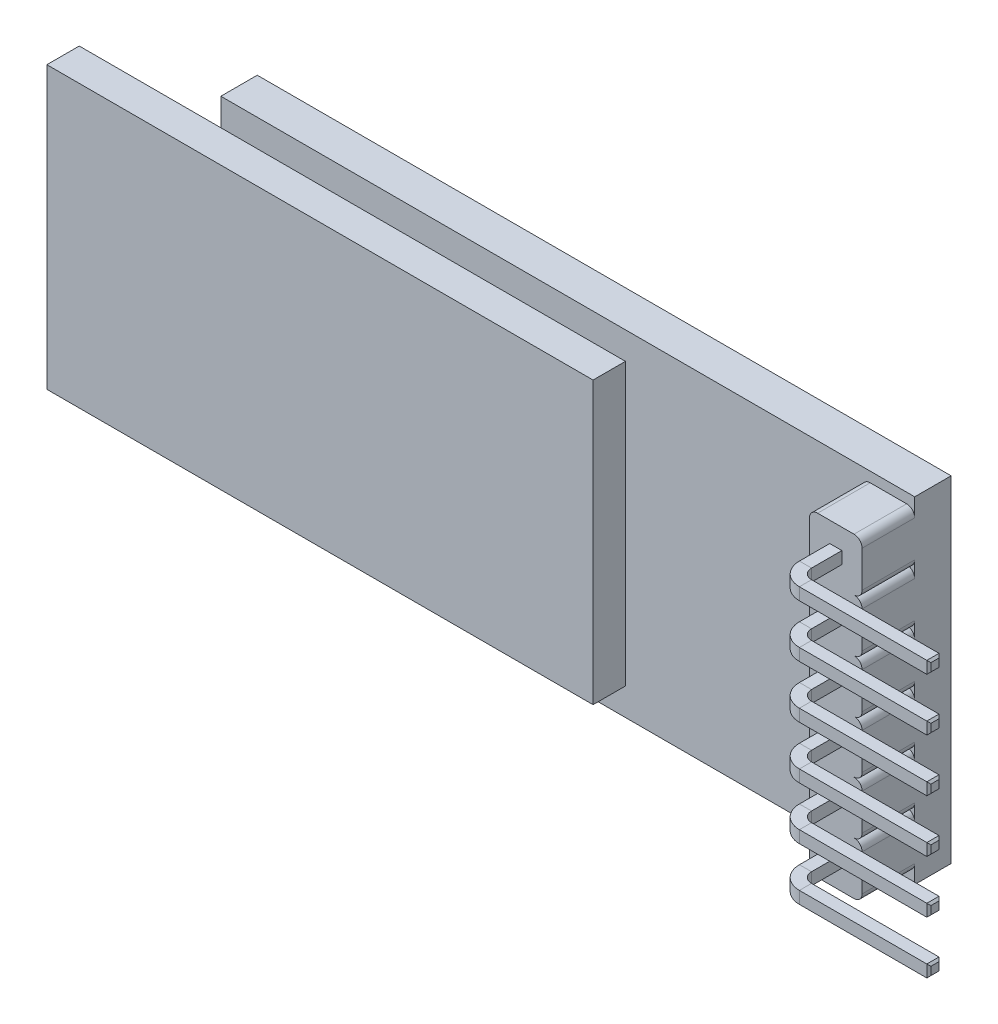
SolidWorks part; units mm, degrees
ref_plane "Front" through (0, 0, 0) normal (0, 0, 1) x (1, 0, 0)
ref_plane "Top" through (0, 0, 0) normal (0, 1, 0) x (1, 0, 0)
ref_plane "Right" through (0, 0, 0) normal (1, 0, 0) x (0, 0, -1)
sketch "Sketch1" plane through (0, 0, 0) normal (0, 0, 1) x (1, 0, 0)
  line L1 (-17.15, -8.3) -> (17.15, -8.3)
  line L2 (-17.15, -8.3) -> (-17.15, 8.3)
  line L3 (-17.15, 8.3) -> (17.15, 8.3)
  line L4 (17.15, -8.3) -> (17.15, 8.3)
  line L5 (-17.15, -8.3) -> (17.15, 8.3) construction
  line L6 (-17.15, 8.3) -> (17.15, -8.3) construction
  point P0 (0, 0)
  dimension "D1" = 16.6
  dimension "D2" = 34.3
extrude "Boss-Extrude1" add sketch "Sketch1" against normal blind 1.8 contours L3 L4 L1 L2
sketch "Sketch2" plane through (0, 0, 0) normal (0, 0, 1) x (1, 0, 0)
  line L0 (-17.15, 0) -> (0, 0) construction
  line L1 (-17.15, -8.3) -> (-17.15, 8.3) construction
  line L2 (0, 0) -> (17.15, 0) construction
  line L3 (17.15, -8.3) -> (17.15, 8.3) construction
  line L5 (-24.15, -6.95) -> (2.85, -6.95)
  line L6 (-24.15, -6.95) -> (-24.15, 6.95)
  line L7 (-24.15, 6.95) -> (2.85, 6.95)
  line L8 (2.85, -6.95) -> (2.85, 6.95)
  line L9 (-24.15, -6.95) -> (2.85, 6.95) construction
  line L10 (-24.15, 6.95) -> (2.85, -6.95) construction
  point P5 (-10.65, 0)
  dimension "D1" = 13.9
  dimension "D2" = 27
  dimension "D3" = 14.3
extrude "Boss-Extrude2" add sketch "Sketch2" along normal blind 1.6 separate body
sketch "Sketch3" plane through (0, 0, 0) normal (0, 0, 1) x (1, 0, 0)
  line L0 (17.15, 0) -> (0, 0) construction
  line L1 (17.15, -8.3) -> (17.15, 8.3) construction
  line L2 (0, 0) -> (17.15, 8.3) construction
  line L3 (17.15, -8.3) -> (0, 0) construction
  line L4 (14.55, 0) -> (14.55, -8.3) construction
  line L5 (-17.15, -8.3) -> (17.15, -8.3) construction
  line L6 (14.95, -2.6) -> (16.75, -2.6)
  line L7 (14.95, 0) -> (16.75, 0)
  line L8 (14.55, -0.4) -> (14.55, -2.2)
  line L9 (14.95, -2.6) -> (16.75, -2.6)
  line L10 (17.15, -0.4) -> (17.15, -2.2)
  line L11 (14.55, -3) -> (14.55, -4.8)
  line L12 (14.95, -5.2) -> (16.75, -5.2)
  line L13 (17.15, -3) -> (17.15, -4.8)
  line L14 (14.95, -5.2) -> (16.75, -5.2)
  line L15 (14.55, -5.6) -> (14.55, -7.4)
  line L16 (14.95, -7.8) -> (16.75, -7.8)
  line L17 (17.15, -5.6) -> (17.15, -7.4)
  arc A0 (16.75, -2.6) -> (17.15, -2.2) centre (16.75, -2.2) ccw
  arc A1 (16.75, 0) -> (17.15, -0.4) centre (16.75, -0.4) cw
  arc A2 (14.95, 0) -> (14.55, -0.4) centre (14.95, -0.4) ccw
  arc A3 (14.95, -2.6) -> (14.55, -2.2) centre (14.95, -2.2) cw
  arc A4 (16.75, -5.2) -> (17.15, -4.8) centre (16.75, -4.8) ccw
  arc A5 (16.75, -2.6) -> (17.15, -3) centre (16.75, -3) cw
  arc A6 (14.95, -2.6) -> (14.55, -3) centre (14.95, -3) ccw
  arc A7 (14.95, -5.2) -> (14.55, -4.8) centre (14.95, -4.8) cw
  arc A8 (16.75, -7.8) -> (17.15, -7.4) centre (16.75, -7.4) ccw
  arc A9 (16.75, -5.2) -> (17.15, -5.6) centre (16.75, -5.6) cw
  arc A10 (14.95, -5.2) -> (14.55, -5.6) centre (14.95, -5.6) ccw
  arc A11 (14.95, -7.8) -> (14.55, -7.4) centre (14.95, -7.4) cw
  point P17 (17.15, -2.6)
  point P26 (14.55, -2.6)
  line M28 (17.15, -8.3) -> (17.15, 8.3)
  dimension "D3" = 0.4
  dimension "D1" = 2.6
  dimension "D2" = 2.6
  dimension "D4" = 3
extrude "Boss-Extrude3" add sketch "Sketch3" along normal blind 2.6 separate body contours A3 L6 A0 A1 L7 A2 L8 M28 | A7 L12 A4 A5 L6 A6 L11 M28 | A11 L16 A8 A9 L12 A10 L15 M28
pattern_linear "LPattern1" count 2 spacing 7.8 along (0, 1, 0) of "Boss-Extrude3"
sketch "Sketch4" plane through (0, 0, 2.6) normal (0, 0, 1) x (1, 0, 0)
  line L0 (14.6672, -5.3172) -> (17.0328, -7.6828) construction
  line L1 (14.6672, -7.6828) -> (17.0328, -5.3172) construction
  line L3 (15.55, -6.8) -> (16.15, -6.8)
  line L4 (15.55, -6.8) -> (15.55, -6.2)
  line L5 (15.55, -6.2) -> (16.15, -6.2)
  line L6 (16.15, -6.8) -> (16.15, -6.2)
  line L7 (15.55, -6.8) -> (16.15, -6.2) construction
  line L8 (15.55, -6.2) -> (16.15, -6.8) construction
  arc A0 (14.95, -5.2) -> (14.55, -5.6) centre (14.95, -5.6) ccw construction
  arc A1 (16.75, -7.8) -> (17.15, -7.4) centre (16.75, -7.4) ccw construction
  arc A2 (14.55, -7.4) -> (14.95, -7.8) centre (14.95, -7.4) ccw construction
  arc A3 (17.15, -5.6) -> (16.75, -5.2) centre (16.75, -5.6) ccw construction
  point P16 (15.85, -6.5)
  dimension "D1" = 0.6
  dimension "D2" = 0.6
ref_plane "Plane1" through (0, -6.5, 0) normal (0, -1, 0) x (-1, 0, 0)
sketch "Sketch5" plane through (0, -6.5, 0) normal (0, -1, 0) x (-1, 0, 0)
  line L0 (-15.85, -2.6) -> (-15.85, -4.1)
  line L1 (-16.65, -4.9) -> (-23.05, -4.9)
  line L2 (-15.85, -2.6) -> (-15.85, 2.9)
  arc A0 (-16.65, -4.9) -> (-15.85, -4.1) centre (-16.65, -4.1) ccw
  point P7 (-15.85, -4.9)
  dimension "D4" = 0.8
  dimension "D1" = 2.3
  dimension "D2" = 7.2
  dimension "D3" = 5.5
ref_plane "Plane2" through (23.05, 0, 0) normal (1, 0, 0) x (0, 0, -1)
sketch "Sketch6" plane through (23.05, 0, 0) normal (1, 0, 0) x (0, 0, -1)
  line L1 (-4.6, -6.8) -> (-5.2, -6.8)
  line L2 (-4.6, -6.8) -> (-4.6, -6.2)
  line L3 (-4.6, -6.2) -> (-5.2, -6.2)
  line L4 (-5.2, -6.8) -> (-5.2, -6.2)
  line L5 (-4.6, -6.8) -> (-5.2, -6.2) construction
  line L6 (-4.6, -6.2) -> (-5.2, -6.8) construction
  point P0 (-4.9, -6.5)
  dimension "D1" = 0.6
  dimension "D2" = 0.6
sweep "Sweep2" add profiles "Sketch6" path "Sketch5"
chamfer "Chamfer1" distance 0.1 angle 45 8 edges at (15.85, -6.2, -2.9) (15.55, -6.5, -2.9) (15.85, -6.8, -2.9) (16.15, -6.5, -2.9) (23.05, -6.5, 4.6) (23.05, -6.2, 4.9) (23.05, -6.5, 5.2) (23.05, -6.8, 4.9)
pattern_linear "LPattern2" count 6 spacing 2.6 along (0, 1, 0) of "Sweep2", "Chamfer1"
